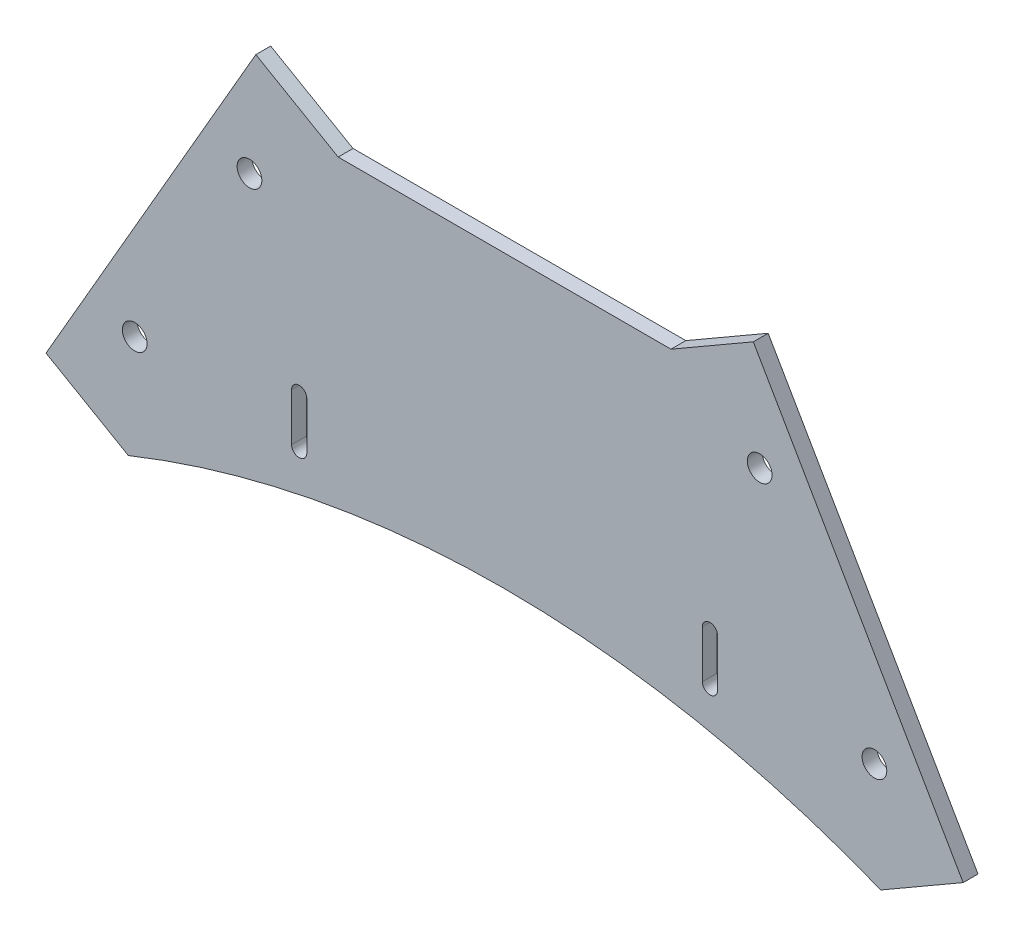
SolidWorks part; units mm, degrees
ref_plane "Front Plane" through (0, 0, 0) normal (0, 0, 1) x (1, 0, 0)
ref_plane "Top Plane" through (0, 0, 0) normal (0, 1, 0) x (1, 0, 0)
ref_plane "Right Plane" through (0, 0, 0) normal (1, 0, 0) x (0, 0, -1)
sketch "Model" plane through (0, 0, 0) normal (0, 0, 1) x (1, 0, 0)
  line L0 (175.591, 0) -> (192.9115, 10)
  line L1 (17.3205, 0) -> (0, 10)
  line L2 (54.8558, 29.1748) -> (54.8558, 19.1748)
  line L3 (141.2558, 29.1748) -> (141.2558, 19.1748)
  line L4 (51.6558, 29.1748) -> (51.6558, 19.1748)
  line L5 (138.0558, 29.1748) -> (138.0558, 19.1748)
  line L9 (61.4558, 76.4445) -> (131.4558, 76.4445)
  line L10 (148.7763, 86.4445) -> (192.9115, 10)
  line L11 (131.4558, 76.4445) -> (148.7763, 86.4445)
  line L12 (44.1352, 86.4445) -> (0, 10)
  line L13 (61.4558, 76.4445) -> (44.1352, 86.4445)
  arc A0 (54.8558, 29.1748) -> (51.6558, 29.1748) centre (53.2558, 29.1748) ccw
  arc A1 (51.6558, 19.1748) -> (54.8558, 19.1748) centre (53.2558, 19.1748) ccw
  arc A2 (138.0558, 19.1748) -> (141.2558, 19.1748) centre (139.6558, 19.1748) ccw
  arc A3 (141.2558, 29.1748) -> (138.0558, 29.1748) centre (139.6558, 29.1748) ccw
  circle A4 centre (42.7955, 64.124) radius 2.6
  circle A5 centre (18.6603, 22.3205) radius 2.6
  circle A6 centre (150.116, 64.124) radius 2.6
  circle A7 centre (174.2512, 22.3205) radius 2.6
  arc A8 (175.591, 0) -> (17.3205, 0) centre (96.4558, -196.7996) ccw
  dimension "D4" = 5.2
  dimension "D5" = 212.1143
  dimension "D12" = 1.6
  dimension "D1" = 20
  dimension "D2" = 88.2705
  dimension "D3" = 70
  dimension "D6" = 86.4
  dimension "D7" = 10
  dimension "D8" = 10
  dimension "D9" = 10
  dimension "D10" = 10
  dimension "D11" = 10
  dimension "D13" = 47.2696
  dimension "D14" = 48.2705
  dimension "D15" = 20
  dimension "D16" = 10
  dimension "D17" = 17.3205
  dimension "D18" = 35.9352
extrude "Boss-Extrude1" add sketch "Model" along normal blind 3.125
